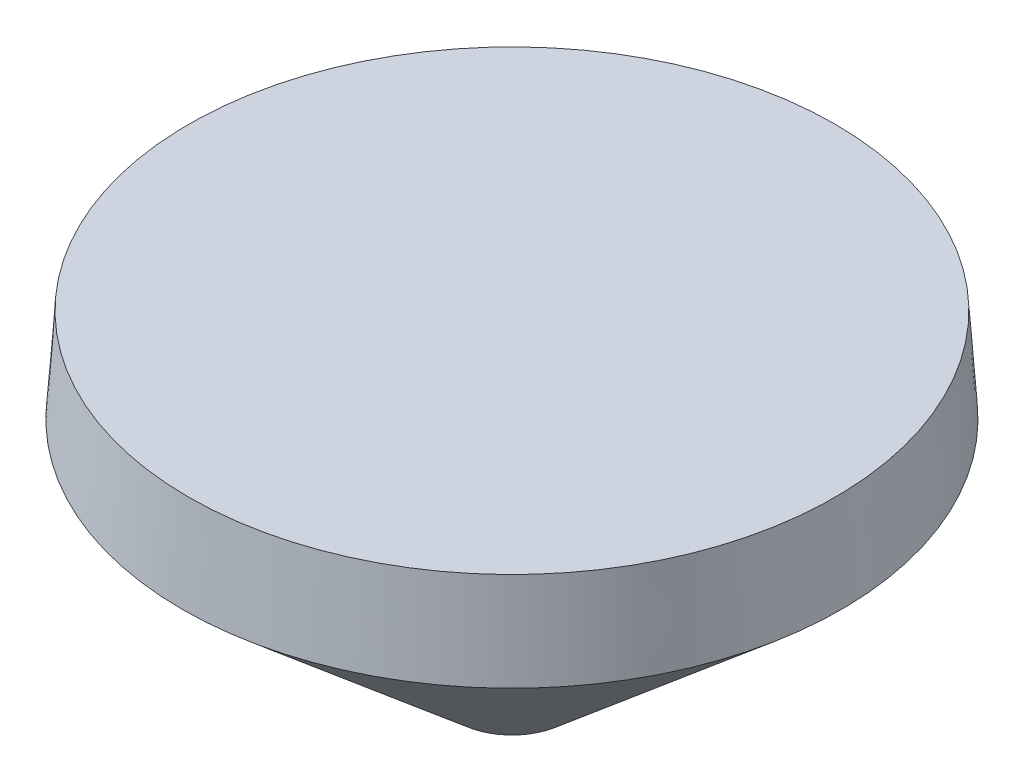
SolidWorks part; units mm, degrees
ref_plane "Alzado" through (0, 0, 0) normal (0, 0, 1) x (1, 0, 0)
ref_plane "Planta" through (0, 0, 0) normal (0, 1, 0) x (1, 0, 0)
ref_plane "Vista lateral" through (0, 0, 0) normal (1, 0, 0) x (0, 0, -1)
sketch "Croquis1" plane through (0, 0, 0) normal (0, 0, 1) x (1, 0, 0)
  line L0 (0, 59.3909) -> (0, 0) construction
  line L1 (0, 42) -> (41.275, 42)
  line L2 (41.275, 42) -> (42.1, 30)
  line L3 (42.1, 30) -> (7, 0)
  line L4 (7, 0) -> (0, 0)
  line L5 (0, 42) -> (0, 0)
  point P1 (41.275, 16.2364)
  point P5 (40.9114, 25.2091)
  point P9 (0, 0)
  point P10 (0, 0)
  point P11 (41.5523, -1.9227)
  point P12 (0, 0)
  point P13 (0, 0)
  point P14 (0, 59.3909)
  point P15 (0, 1.4955)
  point P16 (41.275, 19.4409)
  point P17 (22.325, 0)
  dimension "D1" = 84.2
  dimension "D2" = 82.55
  dimension "D3" = 42
  dimension "D4" = 12
  dimension "D5" = 14
revolve "Revolución1" add sketch "Croquis1" angle 360 about L0
